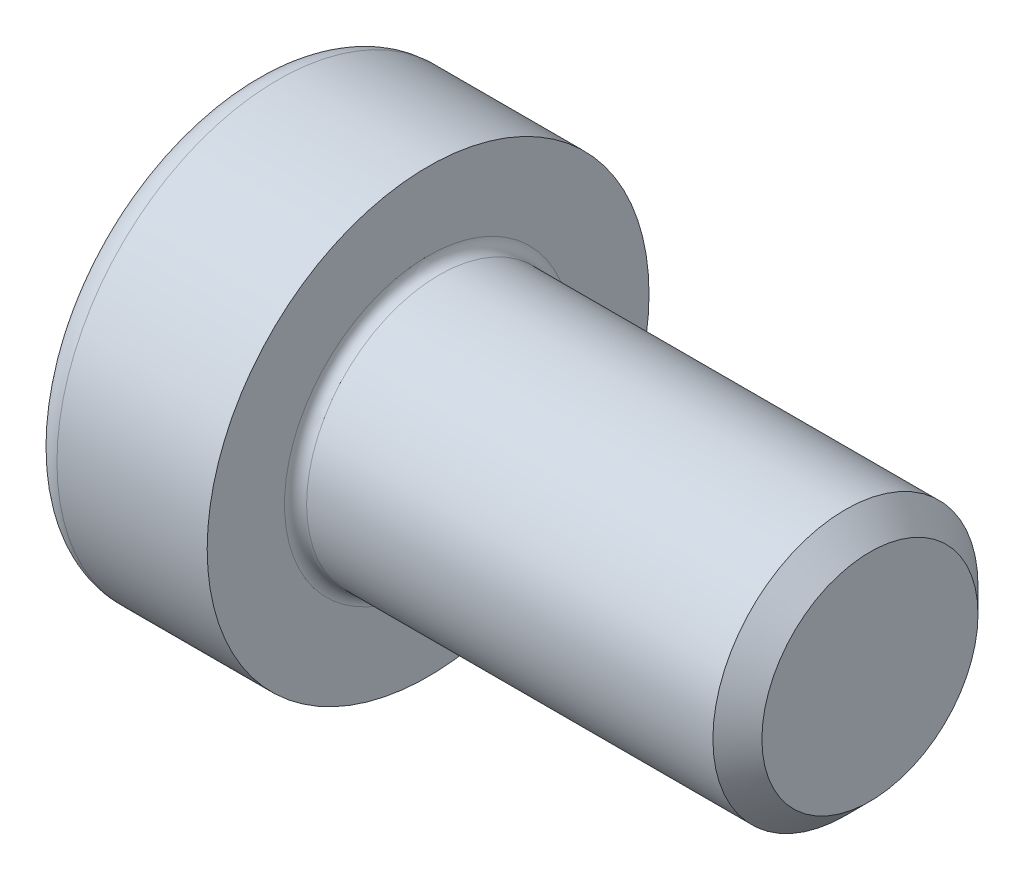
SolidWorks part; units mm, degrees
ref_plane "Plane1" through (0, 0, 0) normal (0, 0, 1) x (1, 0, 0)
ref_plane "Plane2" through (0, 0, 0) normal (0, 1, 0) x (1, 0, 0)
ref_plane "Plane3" through (0, 0, 0) normal (1, 0, 0) x (0, 0, -1)
sketch "BodySke" plane through (0, 0, 0) normal (0, 0, 1) x (1, 0, 0)
  line L0 (0, 0) -> (0, 5)
  line L1 (0, 5) -> (4, 5)
  line L2 (4, 5) -> (4, 3)
  line L3 (4, 3) -> (13.4455, 3)
  line L4 (14, 2.4455) -> (14, 0)
  line L5 (14, 0) -> (0, 0)
  line L6 (-31.75, 0) -> (127, 0) construction
  line L8 (14, 2.4455) -> (13.4455, 3)
  line L10 (14, -2.4455) -> (13.4455, -3) construction
  line L11 (5, 4.525) -> (5, -1.825) construction
  line L12 (7, 4.525) -> (7, -1.825) construction
  line L13 (-46, 4.525) -> (-46, -1.825) construction
  dimension "Diameter" = 6
  dimension "Head_ht" = 4
  dimension "Length" = 10
  dimension "Body_ch_ang" = 45
  dimension "Head_dia" = 10
  dimension "Minor_dia" = 4.891
  dimension "Advance" = 1
  dimension "Thread_nom" = 7
  dimension "Thread_length" = 60
revolve "Base-Revolve" add sketch "BodySke"
cosmetic thread "ThreadCosmetic"
fillet "Fillet1" radius 0.25 1 edges at (4, 0, 3)
fillet "Fillet2" radius 0.6 1 edges at (0, 0, 5)
sketch "Sketch2" plane through (0, 0, 0) normal (0, 0, 1) x (1, 0, 0)
  line L0 (0, 2) -> (3, 2)
  line L1 (3, 2) -> (4.1547, 0)
  line L2 (-31.75, 0) -> (127, 0) construction
  line L3 (4.1547, 0) -> (0, 0)
  line L4 (0, 0) -> (0, 2)
  line L6 (0, 0) -> (47.625, 0) construction
  dimension "D1" = 2
  dimension "D2" = 60
  dimension "Depth" = 3
revolve "Hex-PreBroach" cut sketch "Sketch2" angle 360 about L6
sketch "Sketch3" plane through (0, 0, 0) normal (-1, 0, 0) x (0, 0.5, 0.866)
  line L0 (1.1547, 2) -> (-1.1547, 2)
  line L1 (-1.1547, 2) -> (-2.3094, 0)
  line L2 (1.1547, 2) -> (2.3094, 0)
  line L3 (1.1547, -2) -> (2.3094, 0)
  line L4 (1.1547, -2) -> (-1.1547, -2)
  line L5 (-1.1547, -2) -> (-2.3094, 0)
  dimension "D1" = 2
  dimension "D2" = 2
  dimension "Hex_size" = 4
extrude "Hex" cut sketch "Sketch3" against normal blind 3
sketch "ThdSchSke" plane through (0, 0, 0) normal (0, 0, 1) x (1, 0, 0)
  line L0 (7, -2.4455) -> (6.6117, -3)
  line L1 (7, -2.4455) -> (7.3883, -3)
  line L2 (7.3883, -3) -> (7.3883, -3.75)
  line L3 (-3.175, 0) -> (5.1513, 0) construction
  line L4 (0, 4.4) -> (0, -4.4) construction
  line L5 (7.3883, -3.75) -> (6.6117, -3.75)
  line L6 (6.6117, -3.75) -> (6.6117, -3)
  dimension "Thread_minor" = 4.891
  dimension "Diameter" = 6
  dimension "Start" = 7
  dimension "SideAngle" = 55
  dimension "VeeAngle" = 70
  dimension "Overcut" = 7.5
revolve "ThreadSchematic" [suppressed] cut sketch "ThdSchSke" angle 360 about L3
pattern_linear "ThdSchPat" [suppressed]
equation "\"D2@Sketch3\" = \"Hex_size@Sketch3\" / 2"
equation "\"D1@Sketch3\" = \"Hex_size@Sketch3\" / 2"
equation "\"D1@Sketch2\" = \"Hex_size@Sketch3\" / 2"
equation "\"Thread_minor@ThreadCosmetic\"  =  \"Minor_dia@BodySke\""
equation "\"Depth@Sketch2\" =  \"Key_eng@Hex\""
equation "\"Thread_length@ThreadCosmetic\" = ((sgn( (\"Length@BodySke\" - \"Advance@BodySke\" * 3.0) - \"Thread_nom@BodySke\" )-1)*( (\"Length@BodySke\" - \"Advance@BodySke\" * 3.0) - \"Thread_nom@BodySke\" ))/-2+ \"Thread_nom@BodySke\""
equation "\"Thread_minor@ThdSchSke\" = \"Minor_dia@BodySke\""
equation "\"Diameter@ThdSchSke\" = \"Diameter@BodySke\""
equation "\"Overcut@ThdSchSke\" = \"Diameter@BodySke\" * 1.25"
equation "\"Start@ThdSchSke\" = \"Head_ht@BodySke\" + \"Length@BodySke\" - \"Thread_length@ThreadCosmetic\"  '---Non-countersunk---"
equation "\"Num_threads@ThdSchPat\" = int( \"Thread_length@ThreadCosmetic\" / \"Advance@BodySke\" + 0.999 )  + 1"
equation "\"Advance@ThdSchPat\" = \"Thread_length@ThreadCosmetic\" /  (\"Num_threads@ThdSchPat\" - 1) 'relax it"
equation "\"Num_threads@ThdSchPat\" = \"Num_threads@ThdSchPat\" - sgn( \"Num_threads@ThdSchPat\" - 1) '---chamfered tips only---"
